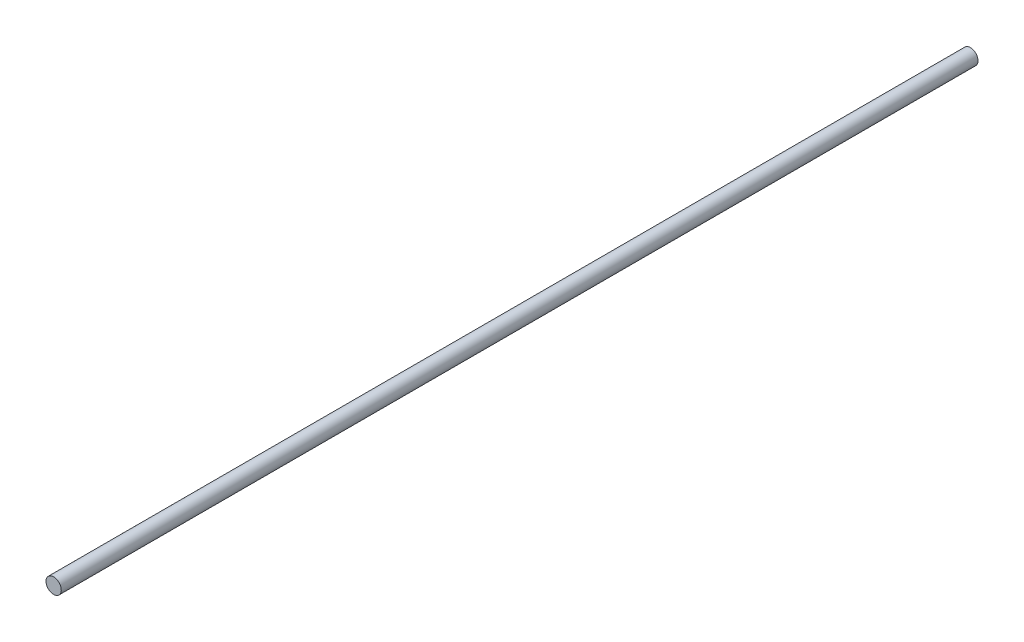
SolidWorks part; units mm, degrees
material "Oak"
ref_plane "Front Plane" through (0, 0, 0) normal (0, 0, 1) x (1, 0, 0)
ref_plane "Top Plane" through (0, 0, 0) normal (0, 1, 0) x (1, 0, 0)
ref_plane "Right Plane" through (0, 0, 0) normal (1, 0, 0) x (0, 0, -1)
sketch "Sketch1" plane through (0, 0, 0) normal (0, 0, 1) x (1, 0, 0)
  circle A0 centre (0, 0) radius 9.525
  dimension "D1" = 19.05
extrude "Boss-Extrude1" add sketch "Sketch1" along normal blind 1143
